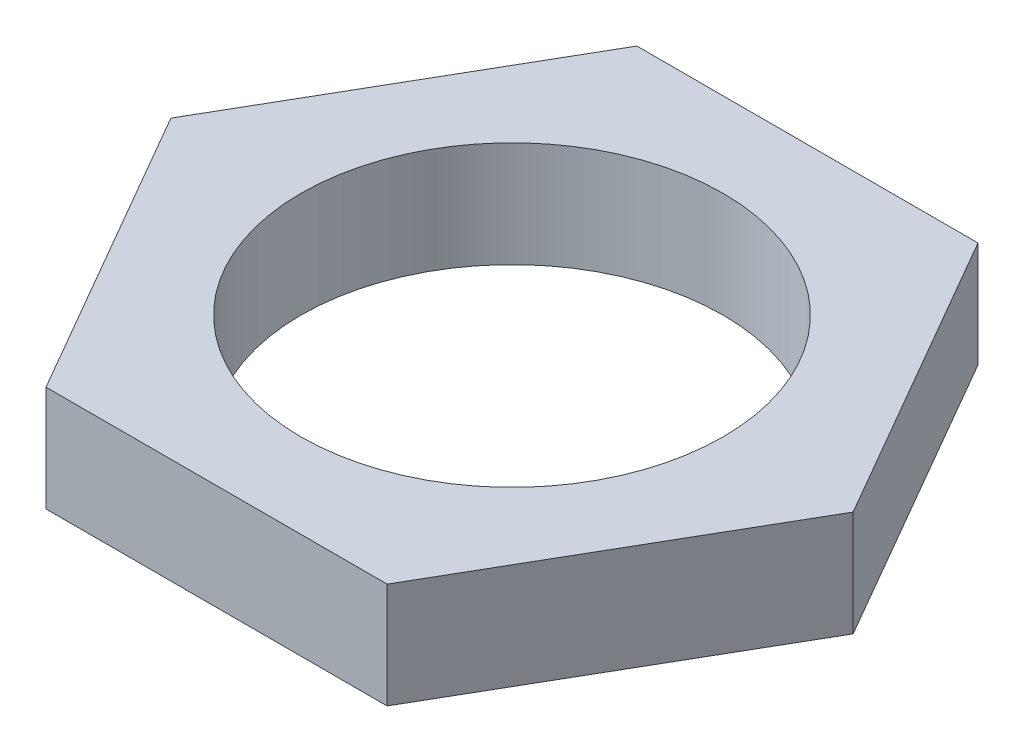
SolidWorks part; units mm, degrees
material "Brass"
ref_plane "Front Plane" through (0, 0, 0) normal (0, 0, 1) x (1, 0, 0)
ref_plane "Top Plane" through (0, 0, 0) normal (0, 1, 0) x (1, 0, 0)
ref_plane "Right Plane" through (0, 0, 0) normal (1, 0, 0) x (0, 0, -1)
sketch "Sketch1" plane through (0, 0, 0) normal (0, 1, 0) x (1, 0, 0)
  line L1 (8.0829, 0) -> (4.0415, 7)
  line L2 (4.0415, 7) -> (-4.0415, 7)
  line L3 (-4.0415, 7) -> (-8.0829, 0)
  line L4 (-8.0829, 0) -> (-4.0415, -7)
  line L5 (-4.0415, -7) -> (4.0415, -7)
  line L6 (4.0415, -7) -> (8.0829, 0)
  circle A0 centre (0, 0) radius 5
  circle A1 centre (0, 0) radius 7 construction
  dimension "D2" = 10
  dimension "D1" = 14
extrude "Boss-Extrude1" add sketch "Sketch1" along normal mid plane 2.5
